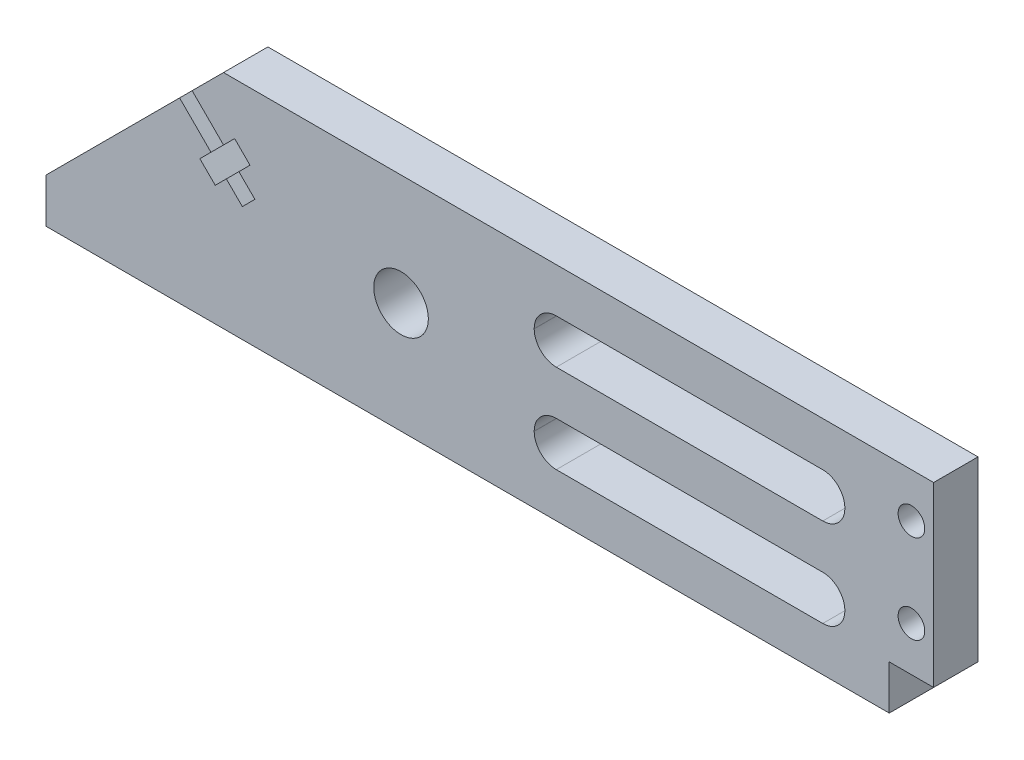
SolidWorks part; units mm, degrees
material "Acrílico (médio-alto impacto)"
ref_plane "Plano frontal" through (0, 0, 0) normal (0, 0, 1) x (1, 0, 0)
ref_plane "Plano superior" through (0, 0, 0) normal (0, 1, 0) x (1, 0, 0)
ref_plane "Plano direito" through (0, 0, 0) normal (1, 0, 0) x (0, 0, -1)
sketch "Esboço1" plane through (0, 0, 0) normal (0, 0, 1) x (1, 0, 0)
  line L0 (-44.7123, -7.9646) -> (-24.7123, 12.0354)
  line L1 (-24.7123, 12.0354) -> (55.2877, 12.0354)
  line L3 (-44.7123, -7.9646) -> (55.2877, -7.9646)
  line L4 (55.2877, 12.0354) -> (55.2877, -7.9646)
  dimension "D1" = 20
  dimension "D3" = 45
extrude "Ressalto-extrusão1" add sketch "Esboço1" along normal blind 5
sketch "Esboço2" plane through (0, -7.9646, 0) normal (0, -1, 0) x (1, 0, 0)
  line L0 (-44.7123, 0) -> (55.2877, 0) construction
  line L1 (-44.7123, 5) -> (50.2877, 5)
  line L2 (-44.7123, 5) -> (-44.7123, 0)
  line L3 (-44.7123, 0) -> (50.2877, 0)
  line L4 (50.2877, 5) -> (50.2877, 0)
  line L5 (55.2877, 5) -> (55.2877, 0) construction
  point P9 (55.2877, 2.5)
  dimension "D1" = 5
extrude "Ressalto-extrusão2" add sketch "Esboço2" along normal blind 5
sketch "Esboço5" plane through (-18.3738, 18.3738, 0) normal (-0.7071, 0.7071, 0) x (0, 0, 1)
  line L0 (0, -8.9639) -> (0, -37.2482) construction
  line L1 (0, -13.9639) -> (5, -13.9639)
  line L2 (0, -13.9639) -> (0, -15.9639)
  line L3 (0, -15.9639) -> (5, -15.9639)
  line L4 (5, -13.9639) -> (5, -15.9639)
  line L5 (5, -8.9639) -> (5, -37.2482) construction
  line L6 (5, -8.9639) -> (0, -8.9639) construction
  dimension "D1" = 2
  dimension "D3" = 5
extrude "Corte-extrusão1" cut sketch "Esboço5" against normal blind 10
sketch "Esboço7" plane through (0, 0, 5) normal (0, 0, 1) x (1, 0, 0)
  line L0 (-24.7123, 4.9643) -> (-23.4607, 6.2159)
  line L1 (-21.1767, 1.4288) -> (-28.2478, 8.4999) construction
  line L2 (-23.4607, 6.2159) -> (-21.7283, 4.4835)
  line L3 (-21.7283, 4.4835) -> (-22.9799, 3.2319)
  line L4 (-22.9799, 3.2319) -> (-24.3941, 1.8177) construction
  line L5 (-22.591, 0.0146) -> (-29.662, 7.0857) construction
  line L6 (-24.7123, 4.9643) -> (-26.1265, 3.5501) construction
  line L7 (-24.7123, 4.9643) -> (-22.9799, 3.2319)
  line L8 (-24.3941, 1.8177) -> (-25.6457, 0.5661)
  line L9 (-26.1265, 3.5501) -> (-27.3781, 2.2985)
  line L10 (-27.3781, 2.2985) -> (-25.6457, 0.5661)
  line L11 (-26.1265, 3.5501) -> (-24.3941, 1.8177)
  line L12 (-25.6457, 0.5661) -> (-41.042, -14.8302) construction
extrude "Corte-extrusão2" cut sketch "Esboço7" against normal blind 10
sketch "Esboço8" plane through (0, 0, 5) normal (0, 0, 1) x (1, 0, 0)
  line L1 (50.2877, -12.9646) -> (-44.7123, -12.9646) construction
  circle A0 centre (-4.7123, -0.4646) radius 3.075
  dimension "D1" = 6.15
  dimension "D2" = 12.5
  dimension "D3" = 40
extrude "Corte-extrusão3" cut sketch "Esboço8" against normal through all
sketch "Esboço9" plane through (0, 0, 5) normal (0, 0, 1) x (1, 0, 0)
  line L0 (50.2877, -12.9646) -> (50.2877, -7.9646) construction
  line L1 (12.7777, 7.0354) -> (42.7977, 7.0354)
  line L2 (10.2877, 4.5454) -> (10.2877, 4.5254)
  line L3 (12.7777, 2.0354) -> (42.7977, 2.0354)
  line L4 (45.2877, 4.5454) -> (45.2877, 4.5254)
  line L5 (12.7777, -2.9646) -> (42.7977, -2.9646)
  line L6 (10.2877, -5.4546) -> (10.2877, -5.4746)
  line L7 (12.7777, -7.9646) -> (42.7977, -7.9646)
  line L8 (45.2877, -5.4546) -> (45.2877, -5.4746)
  line L9 (50.2877, -12.9646) -> (-44.7123, -12.9646) construction
  line L10 (55.2877, 12.0354) -> (-24.7123, 12.0354) construction
  arc A0 (42.7977, 7.0354) -> (45.2877, 4.5454) centre (42.7977, 4.5454) cw
  arc A1 (42.7977, 2.0354) -> (45.2877, 4.5254) centre (42.7977, 4.5254) ccw
  arc A2 (42.7977, -2.9646) -> (45.2877, -5.4546) centre (42.7977, -5.4546) cw
  arc A3 (42.7977, -7.9646) -> (45.2877, -5.4746) centre (42.7977, -5.4746) ccw
  arc A4 (12.7777, -2.9646) -> (10.2877, -5.4546) centre (12.7777, -5.4546) ccw
  arc A5 (10.2877, -5.4746) -> (12.7777, -7.9646) centre (12.7777, -5.4746) ccw
  arc A6 (10.2877, 4.5254) -> (12.7777, 2.0354) centre (12.7777, 4.5254) ccw
  arc A7 (12.7777, 7.0354) -> (10.2877, 4.5454) centre (12.7777, 4.5454) ccw
  point P20 (45.2877, -2.9646)
  point P25 (10.2877, -2.9646)
  dimension "D10" = 2.49
  dimension "D1" = 5
  dimension "D2" = 5
  dimension "D3" = 35
  dimension "D4" = 35
  dimension "D5" = 5
  dimension "D6" = 5
  dimension "D7" = 5
  dimension "D8" = 35
  dimension "D9" = 5
extrude "Corte-extrusão4" cut sketch "Esboço9" against normal blind 10
sketch "Esboço10" plane through (0, 0, 5) normal (0, 0, 1) x (1, 0, 0)
  line L0 (55.2877, -7.9646) -> (55.2877, 12.0354) construction
  line L1 (55.2877, 12.0354) -> (-24.7123, 12.0354) construction
  line L2 (50.2877, -7.9646) -> (55.2877, -7.9646) construction
  circle A0 centre (52.7877, 7.0354) radius 1.5
  circle A1 centre (52.7877, -2.9646) radius 1.5
  dimension "D1" = 3
  dimension "D2" = 3
  dimension "D3" = 2.5
  dimension "D4" = 2.5
  dimension "D5" = 5
  dimension "D6" = 5
extrude "Corte-extrusão5" cut sketch "Esboço10" against normal blind 10
